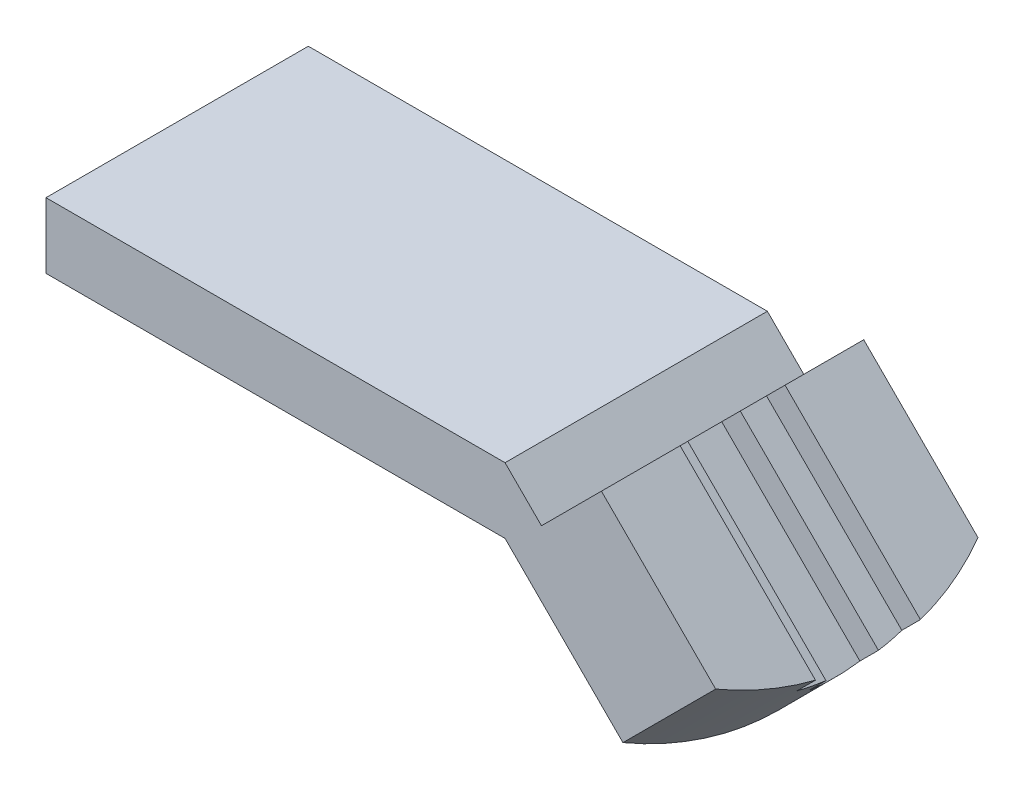
SolidWorks part; units mm, degrees
ref_plane "Front Plane" through (0, 0, 0) normal (0, 0, 1) x (1, 0, 0)
ref_plane "Top Plane" through (0, 0, 0) normal (0, 1, 0) x (1, 0, 0)
ref_plane "Right Plane" through (0, 0, 0) normal (1, 0, 0) x (0, 0, -1)
sketch "Sketch2" plane through (0, 0, 0) normal (0, 0, 1) x (1, 0, 0)
  line L0 (0, 0) -> (35, 0)
  line L1 (0, 0) -> (0, 5)
  line L2 (0, 5) -> (35, 5)
  line L3 (35, 0) -> (45.883, -10.883)
  line L4 (45.883, -10.883) -> (52.9541, -3.812)
  line L5 (52.9541, -3.812) -> (42.3475, 6.7946)
  line L6 (42.3475, 6.7946) -> (37.7764, 2.2236)
  line L7 (37.7764, 2.2236) -> (35, 5)
  line L8 (42.3475, 6.7946) -> (75.6076, 6.7946) construction
  point P8 (0, 0)
  dimension "D1" = 35
  dimension "D2" = 5
  dimension "D3" = 10
  dimension "D4" = 15
  dimension "D5" = 20
  dimension "D6" = 45
extrude "Boss-Extrude1" add sketch "Sketch2" along normal blind 20
sketch "Sketch3" plane through (28.383, -28.383, 0) normal (0.7071, -0.7071, 0) x (0, 0, -1)
  line L0 (-10, 34.7487) -> (-10, -2.9709) construction
  line L1 (-20, 34.7487) -> (0, 34.7487) construction
  line L2 (-14, 34.7487) -> (-14, 32.7487)
  line L3 (-14, 32.7487) -> (-12, 32.7487)
  line L4 (-12, 32.7487) -> (-12, 30.7487)
  line L5 (-12, 30.7487) -> (-8, 30.7487)
  line L6 (-8, 30.7487) -> (-8, 32.7487)
  line L7 (-8, 32.7487) -> (-6, 32.7487)
  line L8 (-6, 32.7487) -> (-6, 34.7487)
  point P6 (-10, 30.7487)
  dimension "D1" = 8
  dimension "D2" = 4
  dimension "D3" = 2
  dimension "D4" = 2
  dimension "D5" = 2
extrude "Cut-Extrude5" cut sketch "Sketch3" against normal through all and the other way through all
sketch "Sketch4" plane through (24.5711, 24.5711, 0) normal (0.7071, 0.7071, 0) x (0, 0, -1)
  line L0 (-20, -40.1397) -> (-20, -25.1397) construction
  line L1 (0, -40.1397) -> (0, -25.1397) construction
  line L2 (-12, -40.1397) -> (-8, -40.1397) construction
  arc A0 (-20, -37.4602) -> (0, -37.4602) centre (-10, -20.1397) ccw
  dimension "D1" = 20
extrude "Cut-Extrude10" cut sketch "Sketch4" against normal through all and the other way through all flip side to cut
